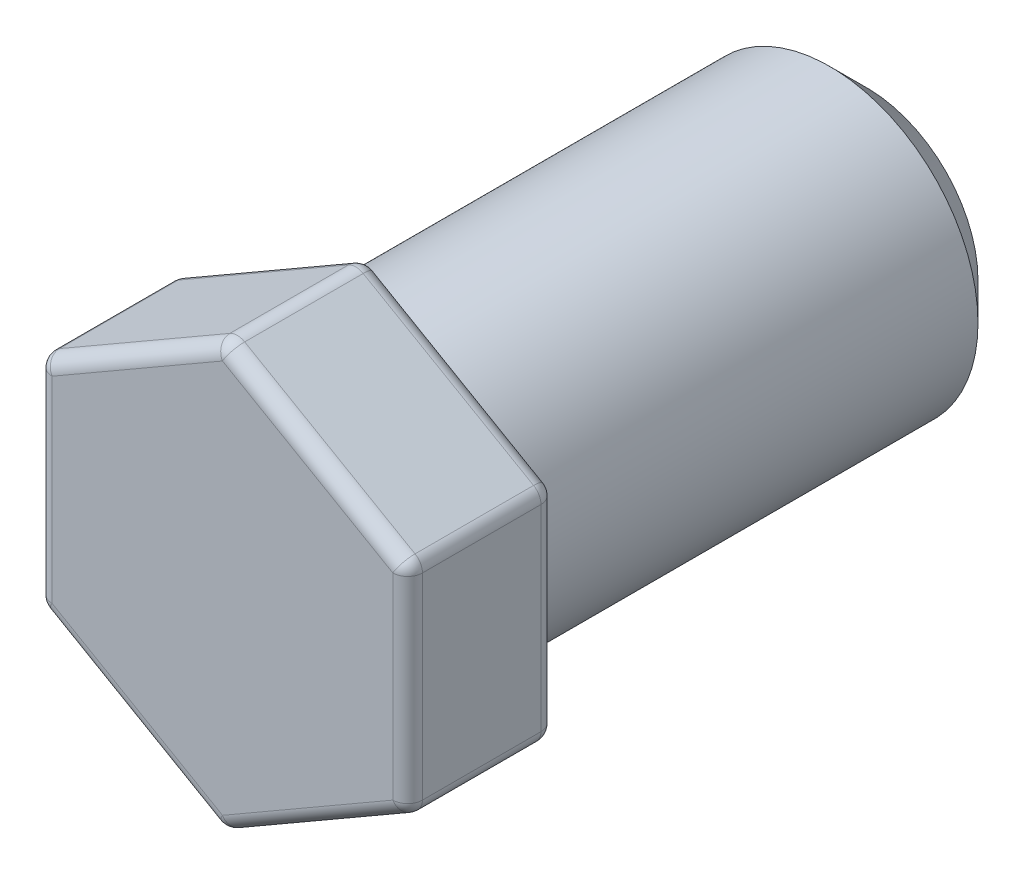
SolidWorks part; units mm, degrees
ref_plane "Front Plane" through (0, 0, 0) normal (0, 0, 1) x (1, 0, 0)
ref_plane "Top Plane" through (0, 0, 0) normal (0, 1, 0) x (1, 0, 0)
ref_plane "Right Plane" through (0, 0, 0) normal (1, 0, 0) x (0, 0, -1)
sketch "Sketch1" plane through (0, 0, 0) normal (0, 0, 1) x (1, 0, 0)
  circle A0 centre (0, 0) radius 2
  dimension "D1" = 4
extrude "Boss-Extrude1" add sketch "Sketch1" along normal mid plane 6.7
sketch "Sketch2" plane through (0, 0, 3.35) normal (0, 0, 1) x (1, 0, 0)
  line L1 (0, -2.8868) -> (2.5, -1.4434)
  line L2 (2.5, -1.4434) -> (2.5, 1.4434)
  line L3 (2.5, 1.4434) -> (0, 2.8868)
  line L4 (0, 2.8868) -> (-2.5, 1.4434)
  line L5 (-2.5, 1.4434) -> (-2.5, -1.4434)
  line L6 (-2.5, -1.4434) -> (0, -2.8868)
  circle A0 centre (0, 0) radius 2.5 construction
  point P1 (0, 0)
  dimension "D1" = 5
extrude "Boss-Extrude2" add sketch "Sketch2" along normal blind 2
fillet "Fillet1" radius 0.2 13 edges at (-2.5, 0, 5.35) (-1.25, 2.1651, 5.35) (1.25, 2.1651, 5.35) (2.5, 0, 5.35) (1.25, -2.1651, 5.35) (-1.25, -2.1651, 5.35) (1.25, -2.1651, 3.35) (2.5, 0, 3.35) (1.25, 2.1651, 3.35) (-1.25, 2.1651, 3.35) (-2.5, 0, 3.35) (-1.25, -2.1651, 3.35) (2, 0, 3.35)
fillet "Fillet2" radius 0.2 18 edges at (-2.4414, -1.4096, 5.2914) (-2.4414, -1.4096, 3.4086) (-2.4414, 1.4096, 5.2914) (-2.4414, 1.4096, 3.4086) (0, 2.8191, 5.2914) (0, 2.8191, 3.4086) (2.4414, -1.4096, 5.2914) (2.4414, -1.4096, 3.4086) (0, -2.8191, 5.2914) (0, -2.8191, 3.4086) (2.4414, 1.4096, 5.2914) (2.4414, 1.4096, 3.4086) (-2.5, -1.4434, 4.35) (-2.5, 1.4434, 4.35) (0, 2.8868, 4.35) (2.5, -1.4434, 4.35) (0, -2.8868, 4.35) (2.5, 1.4434, 4.35)
chamfer "Chamfer1" distance 0.5 angle 45 1 edges at (2, 0, -3.35)
